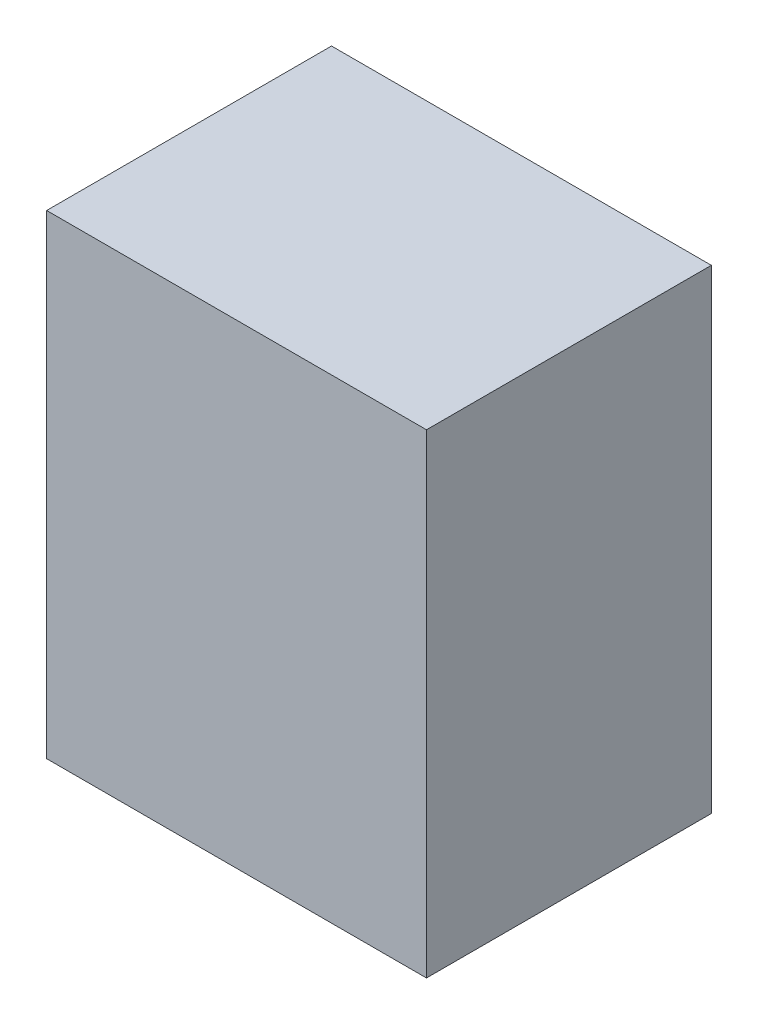
SolidWorks part; units mm, degrees
ref_plane "Plano frontal" through (0, 0, 0) normal (0, 0, 1) x (1, 0, 0)
ref_plane "Plano superior" through (0, 0, 0) normal (0, 1, 0) x (1, 0, 0)
ref_plane "Plano direito" through (0, 0, 0) normal (1, 0, 0) x (0, 0, -1)
sketch "Esboço1" plane through (0, 0, 0) normal (0, 0, 1) x (1, 0, 0)
  line L1 (-20, 25) -> (20, 25)
  line L2 (-20, 25) -> (-20, -25)
  line L3 (-20, -25) -> (20, -25)
  line L4 (20, 25) -> (20, -25)
  line L5 (-20, 25) -> (20, -25) construction
  line L6 (-20, -25) -> (20, 25) construction
  point P0 (0, 0)
  dimension "D1" = 50
  dimension "D2" = 40
extrude "Ressalto-extrusão1" add sketch "Esboço1" along normal blind 30
